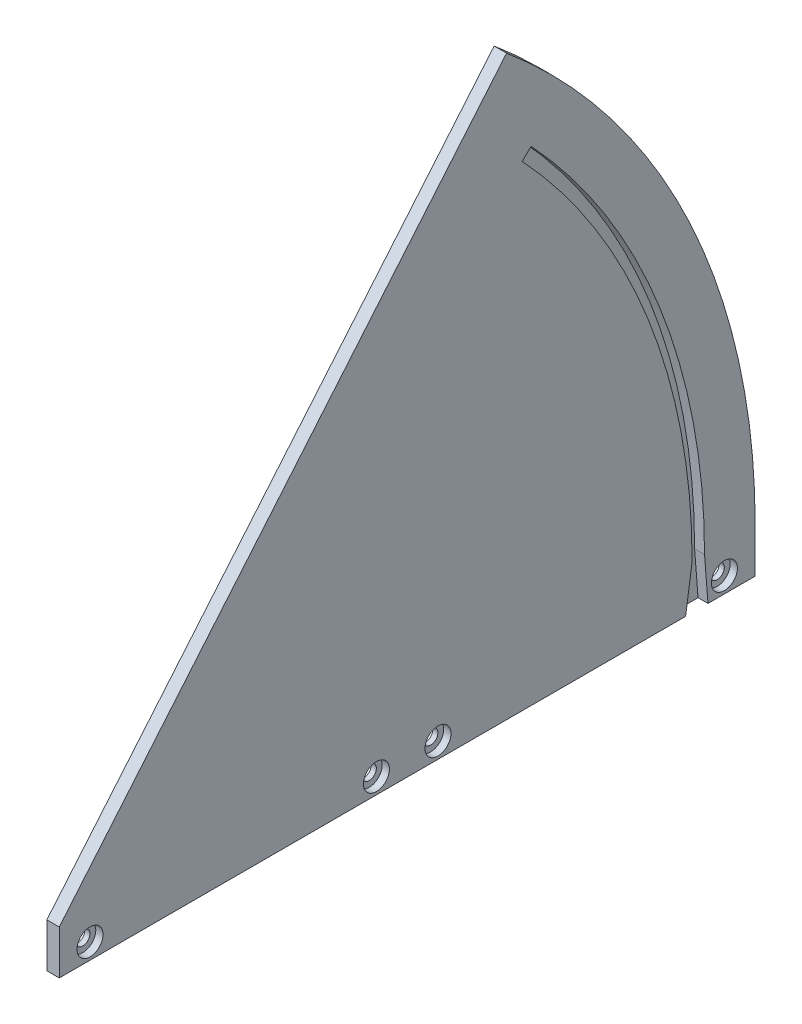
SolidWorks part; units mm, degrees
ref_plane "Front" through (0, 0, 0) normal (0, 0, 1) x (1, 0, 0)
ref_plane "Top" through (0, 0, 0) normal (0, 1, 0) x (1, 0, 0)
ref_plane "Right" through (0, 0, 0) normal (1, 0, 0) x (0, 0, -1)
sketch "Sketch1" plane through (0, 0, 0) normal (1, 0, 0) x (0, 0, -1)
  line L0 (0, 0) -> (178.054, 0)
  line L1 (0, 0) -> (114.4509, 136.3973)
  arc A0 (178.054, 0) -> (114.4509, 136.3973) centre (0, 0) ccw
  dimension "D1" = 356.108
  dimension "D2" = 50
extrude "Boss-Extrude1" add sketch "Sketch1" along normal blind 3.175
sketch "Sketch2" plane through (0, 0, 0) normal (0, -1, 0) x (1, 0, 0)
  line L1 (0, -178.054) -> (3.175, -178.054)
  line L2 (0, -178.054) -> (0, 0)
  line L3 (0, 0) -> (3.175, 0)
  line L4 (3.175, -178.054) -> (3.175, 0)
extrude "Boss-Extrude2" add sketch "Sketch2" along normal blind 11.303
sketch "Sketch3" plane through (3.175, 0, 0) normal (1, 0, 0) x (0, 0, -1)
  line L0 (0, -11.303) -> (7.874, -11.303) construction
  line L1 (178.054, -11.303) -> (0, -11.303) construction
  line L2 (7.874, -11.303) -> (7.874, -7.239) construction
  line L3 (89.027, -11.303) -> (89.027, 106.0982) construction
  line L4 (114.4509, 136.3973) -> (0, 0) construction
  line L5 (89.027, -11.303) -> (81.153, -11.303) construction
  line L6 (81.153, -11.303) -> (81.153, -7.239) construction
  circle A0 centre (7.874, -7.239) radius 1.8288
  circle A1 centre (81.153, -7.239) radius 1.8288
  circle A2 centre (96.901, -7.239) radius 1.8288
  circle A3 centre (170.18, -7.239) radius 1.8288
  dimension "D5" = 3.6576
  dimension "D6" = 3.6576
  dimension "D1" = 7.874
  dimension "D2" = 4.064
  dimension "D3" = 7.874
  dimension "D4" = 4.064
extrude "Cut-Extrude1" cut sketch "Sketch3" against normal through all
sketch "Sketch6" plane through (3.175, 0, 0) normal (1, 0, 0) x (0, 0, -1)
  line L0 (161.53, -11.303) -> (160.26, -11.303) construction
  line L1 (165.1, 0) -> (165.9826, -11.303)
  line L2 (161.53, -11.303) -> (164.7126, -11.303)
  line L3 (178.054, -11.303) -> (0, -11.303) construction
  line L4 (0, 0) -> (120.7465, 112.5979) construction
  line L5 (120.7465, 112.5979) -> (118.4244, 110.4326)
  line L6 (164.7126, -11.303) -> (165.9826, -11.303) construction
  line L7 (0, 0) -> (178.054, 0) construction
  line L8 (165.9826, -11.303) -> (160.26, -11.303)
  line L9 (160.26, -11.303) -> (161.925, 0)
  arc A0 (165.1, 0) -> (120.7465, 112.5979) centre (0, 0) ccw
  arc A1 (161.925, 0) -> (118.4244, 110.4326) centre (0, 0) ccw
  dimension "D1" = 330.2
  dimension "D2" = 3.175
  dimension "D3" = 1.27
  dimension "D4" = 1.27
extrude "Cut-Extrude2" cut sketch "Sketch6" against normal blind 2.54 contours A1 L5 A0 L1 L8 L9
sketch "Sketch8" plane through (3.175, 0, 0) normal (1, 0, 0) x (0, 0, -1)
  circle A0 centre (7.874, -7.239) radius 3.3274
  circle A1 centre (81.153, -7.239) radius 3.3274
  circle A2 centre (96.901, -7.239) radius 3.3274
  circle A3 centre (170.18, -7.239) radius 3.3274
  dimension "D1" = 6.6548
  dimension "D2" = 6.6548
  dimension "D3" = 6.6548
  dimension "D4" = 6.6548
extrude "Cut-Extrude3" cut sketch "Sketch8" against normal blind 1.8542
